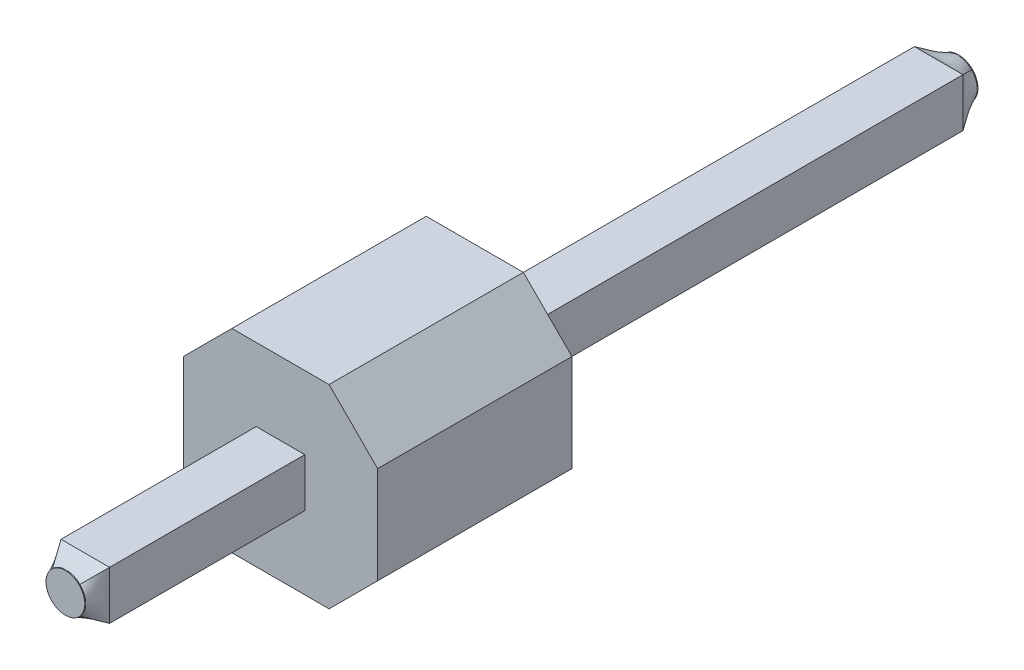
SolidWorks part; units mm, degrees
ref_plane "Front Plane" through (0, 0, 0) normal (0, 0, 1) x (1, 0, 0)
ref_plane "Top Plane" through (0, 0, 0) normal (0, 1, 0) x (1, 0, 0)
ref_plane "Right Plane" through (0, 0, 0) normal (1, 0, 0) x (0, 0, -1)
ref_plane "Plane1" through (0, 0, 5.092) normal (0, 0, 1) x (1, 0, 0)
ref_plane "Plane2" through (0, 0, 5.342) normal (0, 0, 1) x (1, 0, 0)
sketch "Sketch1" plane through (0, 0, 5.092) normal (0, 0, 1) x (1, 0, 0)
  line L1 (-0.3175, -0.3175) -> (0.3175, -0.3175)
  line L2 (-0.3175, -0.3175) -> (-0.3175, 0.3175)
  line L3 (-0.3175, 0.3175) -> (0.3175, 0.3175)
  line L4 (0.3175, -0.3175) -> (0.3175, 0.3175)
  line L5 (-0.3175, -0.3175) -> (0.3175, 0.3175) construction
  line L6 (-0.3175, 0.3175) -> (0.3175, -0.3175) construction
  point P0 (0, 0)
  dimension "D1" = 0.635
  dimension "D2" = 0.635
extrude "Boss-Extrude1" add sketch "Sketch1" against normal blind 11.157
sketch "Sketch2" plane through (0, 0, 0) normal (0, 0, 1) x (1, 0, 0)
  line L0 (-1.27, 0.635) -> (-0.635, 1.27)
  line L1 (-0.635, -1.27) -> (0.635, -1.27)
  line L2 (-1.27, -0.635) -> (-1.27, 0.635)
  line L3 (-0.635, 1.27) -> (0.635, 1.27)
  line L4 (1.27, -0.635) -> (1.27, 0.635)
  line L5 (-1.27, -1.27) -> (1.27, 1.27) construction
  line L6 (-1.27, 1.27) -> (1.27, -1.27) construction
  line L7 (-0.635, -1.27) -> (-1.27, -0.635)
  line L8 (0.635, -1.27) -> (1.27, -0.635)
  line L9 (1.27, 0.635) -> (0.635, 1.27)
  point P0 (0, 0)
  dimension "D1" = 2.54
  dimension "D2" = 2.54
extrude "Boss-Extrude2" add sketch "Sketch2" along normal blind 2.54
sketch "Sketch3" plane through (0, 0, 5.342) normal (0, 0, 1) x (1, 0, 0)
  circle A0 centre (0, 0) radius 0.254
  dimension "D1" = 0.508
loft "Loft1" add profiles "Sketch3" section "Sketch3" section face at (0, 0, 5.092)
ref_plane "Plane3" through (0, 0, -6.315) normal (0, 0, -1) x (-1, 0, 0)
sketch "Sketch4" plane through (0, 0, -6.315) normal (0, 0, -1) x (-1, 0, 0)
  circle A0 centre (0, 0) radius 0.254
  dimension "D1" = 0.508
loft "Loft2" add profiles "Sketch4" section "Sketch4" section face at (0, 0, -6.065)
sketch "Sketch6" plane through (0, 0, 5.342) normal (0, 0, 1) x (1, 0, 0)
  circle A0 centre (0, 0) radius 0.254
  dimension "D1" = 0.508
extrude "Boss-Extrude3" add sketch "Sketch6" along normal blind 0.01
sketch "Sketch7" plane through (0, 0, -6.315) normal (0, 0, -1) x (-1, 0, 0)
  circle A0 centre (0, 0) radius 0.254
extrude "Boss-Extrude4" add sketch "Sketch7" along normal blind 0.01
